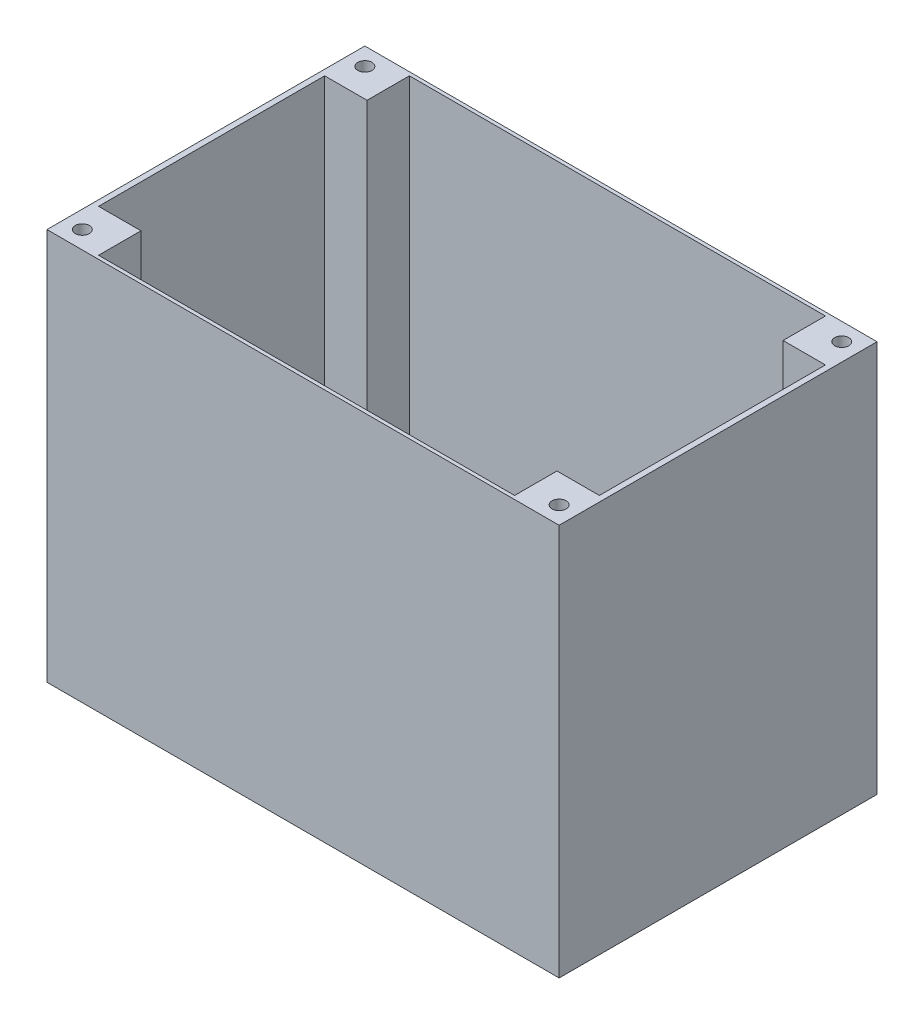
SolidWorks part; units mm, degrees
ref_plane "Front Plane" through (0, 0, 0) normal (0, 0, 1) x (1, 0, 0)
ref_plane "Top Plane" through (0, 0, 0) normal (0, 1, 0) x (1, 0, 0)
ref_plane "Right Plane" through (0, 0, 0) normal (1, 0, 0) x (0, 0, -1)
sketch "Sketch3" plane through (0, 0, 0) normal (0, 1, 0) x (1, 0, 0)
  line L1 (72.5, -45) -> (-72.5, -45)
  line L2 (72.5, -45) -> (72.5, 45)
  line L3 (72.5, 45) -> (-72.5, 45)
  line L4 (-72.5, -45) -> (-72.5, 45)
  line L5 (72.5, -45) -> (-72.5, 45) construction
  line L6 (72.5, 45) -> (-72.5, -45) construction
  line L7 (70.8889, -44) -> (-70.8889, -44)
  line L8 (70.8889, -44) -> (70.8889, 44)
  line L9 (70.8889, 44) -> (-70.8889, 44)
  line L10 (-70.8889, -44) -> (-70.8889, 44)
  line L11 (70.8889, -44) -> (-70.8889, 44) construction
  line L12 (70.8889, 44) -> (-70.8889, -44) construction
  point P0 (0, 0)
  point P6 (0, 0)
  dimension "D1" = 145
  dimension "D2" = 90
  dimension "D3" = 1
extrude "Boss-Extrude1" add sketch "Sketch3" along normal blind 110
sketch "Sketch4" plane through (0, 0, 0) normal (0, -1, 0) x (1, 0, 0)
  line L4 (-72.5, 45) -> (-72.5, -45)
  line L5 (-72.5, -45) -> (72.5, -45)
  line L6 (72.5, -45) -> (72.5, 45)
  line L7 (72.5, 45) -> (-72.5, 45)
  line L8 (-72.5, 45) -> (-72.5, -45)
  line L9 (-72.5, -45) -> (72.5, -45)
  line L10 (72.5, -45) -> (72.5, 45)
  line L11 (72.5, 45) -> (-72.5, 45)
  dimension "D1" = 0
extrude "Boss-Extrude2" add sketch "Sketch4" along normal blind 1
sketch "Sketch5" plane through (0, 0, 0) normal (0, 1, 0) x (1, 0, 0)
  line L1 (-70.8889, 44) -> (-58.8889, 44)
  line L2 (-70.8889, 44) -> (-70.8889, 32)
  line L3 (-70.8889, 32) -> (-58.8889, 32)
  line L4 (-58.8889, 44) -> (-58.8889, 32)
  line L5 (70.8889, 44) -> (58.8889, 44)
  line L6 (70.8889, 44) -> (70.8889, 32)
  line L7 (70.8889, 32) -> (58.8889, 32)
  line L8 (58.8889, 44) -> (58.8889, 32)
  line L9 (70.8889, -44) -> (58.8889, -44)
  line L10 (70.8889, -44) -> (70.8889, -32)
  line L11 (70.8889, -32) -> (58.8889, -32)
  line L12 (58.8889, -44) -> (58.8889, -32)
  line L13 (-70.8889, -44) -> (-58.8889, -44)
  line L14 (-70.8889, -44) -> (-70.8889, -32)
  line L15 (-70.8889, -32) -> (-58.8889, -32)
  line L16 (-58.8889, -44) -> (-58.8889, -32)
  dimension "D1" = 12
extrude "Boss-Extrude3" add sketch "Sketch5" along normal up to surface (110 mm away) up to face at (0, 110, 0)
sketch "Sketch6" plane through (0, 110, 0) normal (0, 1, 0) x (1, 0, 0)
  line L0 (-69.074, 41.2339) -> (-66.1951, 38.4843) construction
  line L1 (-58.8889, 32) -> (-70.8889, 32) construction
  line L2 (-70.8889, 32) -> (-58.8889, 32) construction
  line L3 (-70.8889, 32) -> (-58.8889, 32) construction
  line L4 (-68.9142, 38.5858) -> (-66.0858, 41.4142) construction
  line L5 (0, 0) -> (0, -50000) construction
  line L6 (0, 0) -> (50000, 0) construction
  line L7 (72.5, 45) -> (-72.5, 45) construction
  line L8 (-72.5, 45) -> (-72.5, -45) construction
  circle A0 centre (-67.5, 40) radius 2
  circle A1 centre (-67.5, -40) radius 2
  circle A2 centre (67.5, -40) radius 2
  circle A3 centre (67.5, 40) radius 2
  dimension "D1" = 4
  dimension "D2" = 5
  dimension "D3" = 5
extrude "Cut-Extrude1" cut sketch "Sketch6" against normal blind 12
sketch "Sketch7" plane through (0, 0, 0) normal (0, 1, 0) x (1, 0, 0)
  circle A0 centre (0, 0) radius 10
  dimension "D1" = 20
extrude "Cut-Extrude2" cut sketch "Sketch7" against normal blind 12
